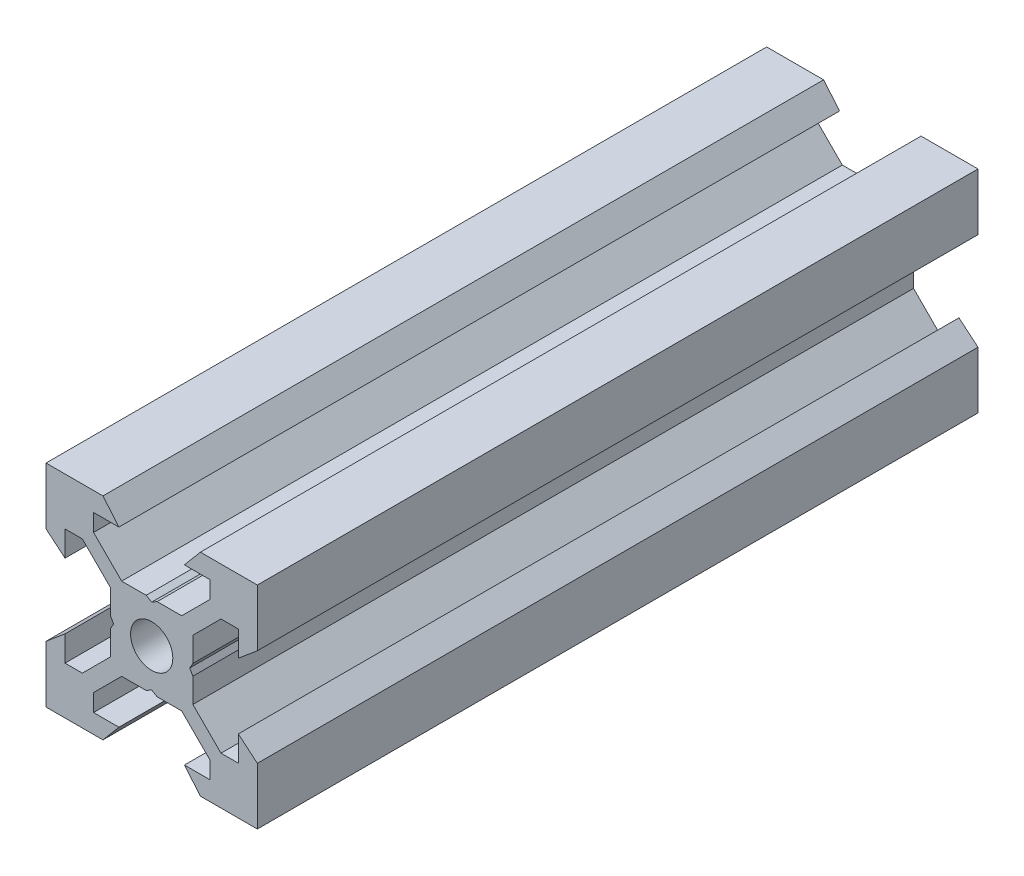
SolidWorks part; units mm, degrees
ref_plane "Front Plane" through (0, 0, 0) normal (0, 0, 1) x (1, 0, 0)
ref_plane "Top Plane" through (0, 0, 0) normal (0, 1, 0) x (1, 0, 0)
ref_plane "Right Plane" through (0, 0, 0) normal (1, 0, 0) x (0, 0, -1)
sketch "Sketch1" plane through (0, 0, 0) normal (0, 0, 1) x (1, 0, 0)
  line L0 (10, 10) -> (4.6104, 10) construction
  line L1 (10, 10) -> (10, 4.6104) construction
  line L2 (10, -10) -> (10, -4.6104) construction
  line L3 (10, -10) -> (4.6104, -10) construction
  line L4 (10, 10) -> (10, 4.6104)
  line L5 (6.5607, 5.5) -> (8.2, 5.5)
  line L6 (5.5, 8.2) -> (5.5, 6.5607)
  line L7 (10, 10) -> (4.6104, 10)
  line L8 (10, 10) -> (10, 4.6104)
  line L9 (6.5607, 5.5) -> (3.9, 2.8393)
  line L10 (5.5, 6.5607) -> (2.8393, 3.9)
  line L11 (10, 4.6104) -> (8.2, 3.1)
  line L12 (4.6104, 10) -> (3.1, 8.2)
  line L13 (8.2, 3.1) -> (8.2, 5.5)
  line L14 (3.1, 8.2) -> (5.5, 8.2)
  line L15 (-6.5607, 5.5) -> (-8.2, 5.5)
  line L16 (6.5607, -5.5) -> (8.2, -5.5)
  line L17 (3.1, -8.2) -> (5.5, -8.2)
  line L18 (8.2, -3.1) -> (8.2, -5.5)
  line L19 (4.6104, -10) -> (3.1, -8.2)
  line L20 (10, -4.6104) -> (8.2, -3.1)
  line L21 (0.5196, -3.9) -> (0, -3.6)
  line L22 (0.5196, 3.9) -> (0, 3.6)
  line L23 (3.6, 0) -> (3.9, -0.5196)
  line L24 (3.9, 0.5196) -> (3.6, 0)
  line L25 (3.9, 0.5196) -> (3.9, 2.8393)
  line L26 (2.8393, 3.9) -> (0.5196, 3.9)
  line L27 (3.9, -2.8393) -> (3.9, -0.5196)
  line L28 (2.8393, -3.9) -> (0.5196, -3.9)
  line L29 (5.5, -6.5607) -> (2.8393, -3.9)
  line L30 (6.5607, -5.5) -> (3.9, -2.8393)
  line L31 (10, -10) -> (10, -4.6104)
  line L32 (10, -10) -> (4.6104, -10)
  line L33 (5.5, -8.2) -> (5.5, -6.5607)
  line L34 (-6.5607, -5.5) -> (-8.2, -5.5)
  line L35 (10, -10) -> (10, -4.6104)
  line L36 (0, 0) -> (0, 8.2) construction
  line L37 (-10, -10) -> (-4.6104, -10) construction
  line L38 (-10, -10) -> (-10, -4.6104) construction
  line L39 (-10, 10) -> (-10, 4.6104) construction
  line L40 (-10, 10) -> (-4.6104, 10) construction
  line L41 (-10, -10) -> (-10, -4.6104)
  line L43 (-5.5, -8.2) -> (-5.5, -6.5607)
  line L44 (-10, -10) -> (-4.6104, -10)
  line L45 (-10, -10) -> (-10, -4.6104)
  line L46 (-6.5607, -5.5) -> (-3.9, -2.8393)
  line L47 (-5.5, -6.5607) -> (-2.8393, -3.9)
  line L48 (-2.8393, -3.9) -> (-0.5196, -3.9)
  line L49 (-3.9, -2.8393) -> (-3.9, -0.5196)
  line L50 (-2.8393, 3.9) -> (-0.5196, 3.9)
  line L51 (-3.9, 0.5196) -> (-3.9, 2.8393)
  line L52 (-3.9, 0.5196) -> (-3.6, 0)
  line L53 (-3.6, 0) -> (-3.9, -0.5196)
  line L54 (-0.5196, 3.9) -> (0, 3.6)
  line L55 (-0.5196, -3.9) -> (0, -3.6)
  line L56 (-10, -4.6104) -> (-8.2, -3.1)
  line L57 (-4.6104, -10) -> (-3.1, -8.2)
  line L58 (-8.2, -3.1) -> (-8.2, -5.5)
  line L59 (-3.1, -8.2) -> (-5.5, -8.2)
  line L60 (-10, -10) -> (10, -10) construction
  line L61 (-10, -10) -> (-10, 10) construction
  line L62 (-3.1, 8.2) -> (-5.5, 8.2)
  line L63 (-8.2, 3.1) -> (-8.2, 5.5)
  line L64 (-4.6104, 10) -> (-3.1, 8.2)
  line L65 (-10, 4.6104) -> (-8.2, 3.1)
  line L66 (-5.5, 6.5607) -> (-2.8393, 3.9)
  line L67 (-6.5607, 5.5) -> (-3.9, 2.8393)
  line L68 (-10, 10) -> (-10, 4.6104)
  line L69 (-10, 10) -> (-4.6104, 10)
  line L70 (-5.5, 8.2) -> (-5.5, 6.5607)
  line L71 (-10, 10) -> (10, 10) construction
  line L72 (-10, 10) -> (-10, 4.6104)
  line L73 (10, -10) -> (10, 10) construction
  line L74 (-10, -10) -> (10, 10) construction
  line L75 (-10, 10) -> (10, -10) construction
  circle A0 centre (0, 0) radius 2
  dimension "D7" = 4
  dimension "D1" = 20
  dimension "D2" = 5.3896
  dimension "D3" = 4.5
  dimension "D4" = 50
  dimension "D5" = 1.8
  dimension "D6" = 1.5104
  dimension "D8" = 5.5
  dimension "D9" = 120
  dimension "D10" = 0.3
  dimension "D11" = 2.3197
  dimension "D12" = 7.8
  dimension "D13" = 7.8
  dimension "D14" = 1.5
  dimension "D15" = 2.6607
extrude "Boss-Extrude1" add sketch "Sketch1" along normal mid plane 68.2 contours L70 L62 L64 L69 L68 L65 L63 L15 L67 L51 L52 L53 L49 L46 L34 L58 L56 L41 L44 L57 L59 L43 L47 L48 L55 L21 L28 L29 L33 L17 L19 L32 L31 L20 L18 L16 L30 L27 L23 L24 L25 L9 L5 L13 L11 L4 L7 L12 L14 L6 L10
